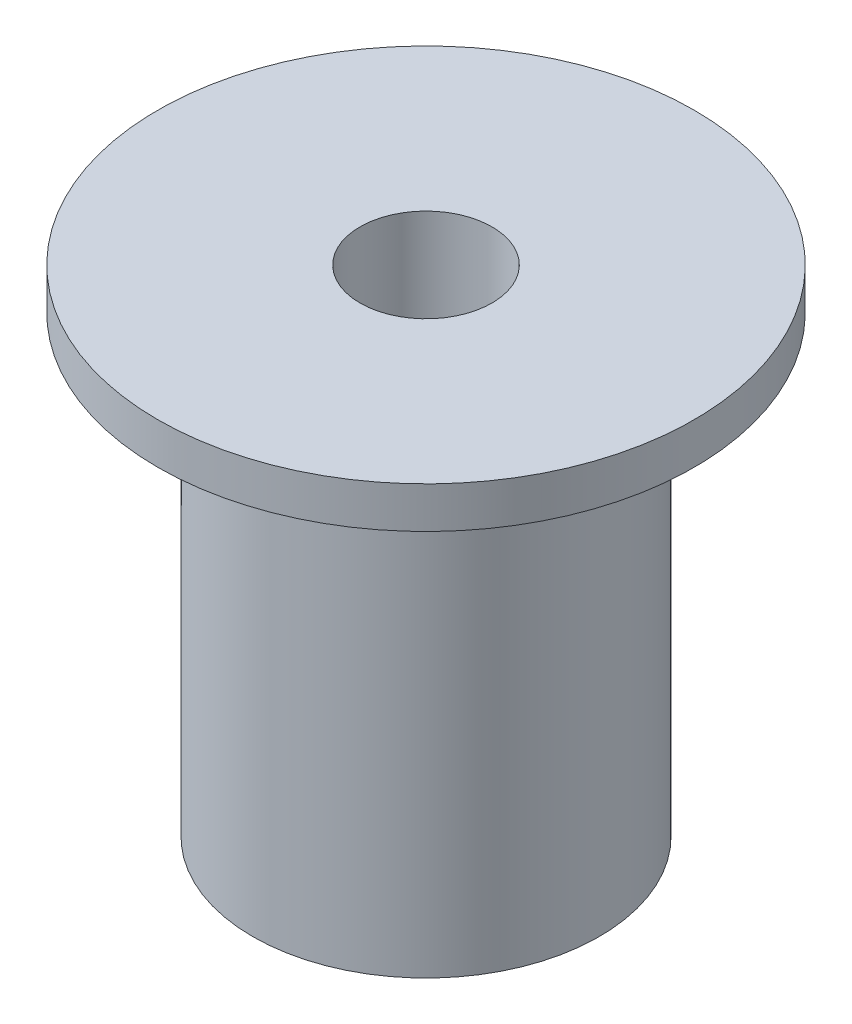
SolidWorks part; units mm, degrees
ref_plane "Front Plane" through (0, 0, 0) normal (0, 0, 1) x (1, 0, 0)
ref_plane "Top Plane" through (0, 0, 0) normal (0, 1, 0) x (1, 0, 0)
ref_plane "Right Plane" through (0, 0, 0) normal (1, 0, 0) x (0, 0, -1)
sketch "Sketch1" plane through (0, 0, 0) normal (0, 1, 0) x (1, 0, 0)
  circle A0 centre (0, 0) radius 4.2
  circle A1 centre (0, 0) radius 1.6
  dimension "D1" = 8.4
  dimension "D2" = 3.2
extrude "Boss-Extrude1" add sketch "Sketch1" along normal blind 11
sketch "Sketch2" plane through (0, 11, 0) normal (0, 1, 0) x (1, 0, 0)
  circle A0 centre (0, 0) radius 6.5
  circle A1 centre (0, 0) radius 1.6
  dimension "D1" = 13
extrude "Boss-Extrude2" add sketch "Sketch2" along normal blind 1
